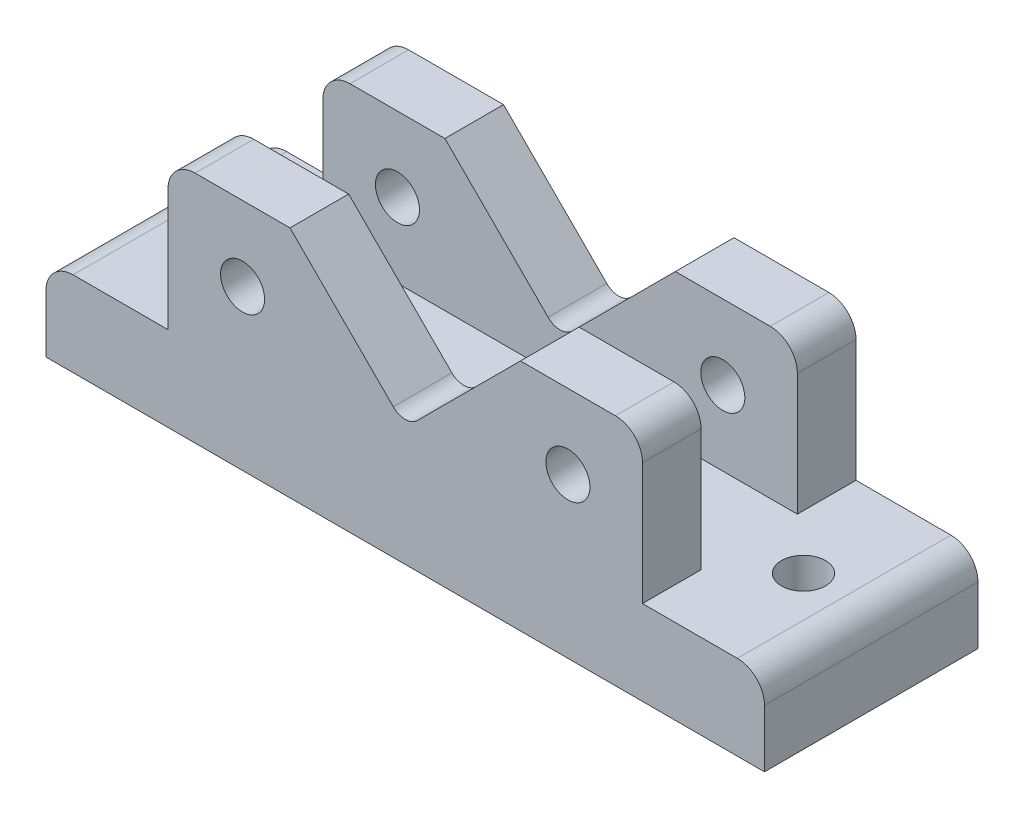
SolidWorks part; units mm, degrees
ref_plane "Front Plane" through (0, 0, 0) normal (0, 0, 1) x (1, 0, 0)
ref_plane "Top Plane" through (0, 0, 0) normal (0, 1, 0) x (1, 0, 0)
ref_plane "Right Plane" through (0, 0, 0) normal (1, 0, 0) x (0, 0, -1)
sketch "Sketch1" plane through (0, 0, 0) normal (0, 1, 0) x (1, 0, 0)
  line L0 (0, 0) -> (0, -31.5) construction
  line L1 (-106, 31.5) -> (106, 31.5)
  line L2 (-106, 31.5) -> (-106, -31.5)
  line L3 (-106, -31.5) -> (106, -31.5)
  line L4 (106, 31.5) -> (106, -31.5)
  line L5 (-106, 31.5) -> (106, -31.5) construction
  line L6 (-106, -31.5) -> (106, 31.5) construction
  circle A0 centre (86, 0) radius 6.5
  circle A1 centre (-86, 0) radius 6.5
  point P0 (0, 0)
  dimension "D5" = 13
  dimension "D1" = 63
  dimension "D2" = 212
  dimension "D3" = 86
  dimension "D4" = 31.5
extrude "Boss-Extrude1" add sketch "Sketch1" along normal blind 25
sketch "Sketch2" plane through (0, 0, 31.5) normal (0, 0, 1) x (1, 0, 0)
  line L0 (-106, 25) -> (106, 25) construction
  line L1 (-70, 25) -> (70, 25)
  line L2 (-70, 25) -> (-70, 61)
  line L3 (-62, 69) -> (-34, 69)
  line L4 (-34, 69) -> (0, 35)
  line L5 (0, 0) -> (0, 79.4574) construction
  line L6 (34, 69) -> (0, 35)
  line L7 (62, 69) -> (34, 69)
  line L8 (70, 25) -> (70, 61)
  arc A0 (-62, 69) -> (-70, 61) centre (-62, 61) ccw
  circle A1 centre (-48, 47) radius 6.5
  arc A2 (62, 69) -> (70, 61) centre (62, 61) cw
  circle A3 centre (48, 47) radius 6.5
  point P11 (-70, 69)
  dimension "D6" = 8
  dimension "D7" = 13
  dimension "D1" = 36
  dimension "D2" = 44
  dimension "D3" = 70
  dimension "D4" = 45
  dimension "D8" = 22
  dimension "D9" = 48
extrude "Boss-Extrude2" add sketch "Sketch2" against normal blind 17.3
mirror "Mirror1" about plane through (0, 0, 0) normal (0, 0, 1) of "Boss-Extrude2"
fillet "Fillet1" radius 8 2 edges at (-106, 25, 0) (106, 25, 0)
fillet "Fillet2" radius 5 2 edges at (0, 35, 22.85) (0, 35, -22.85)
